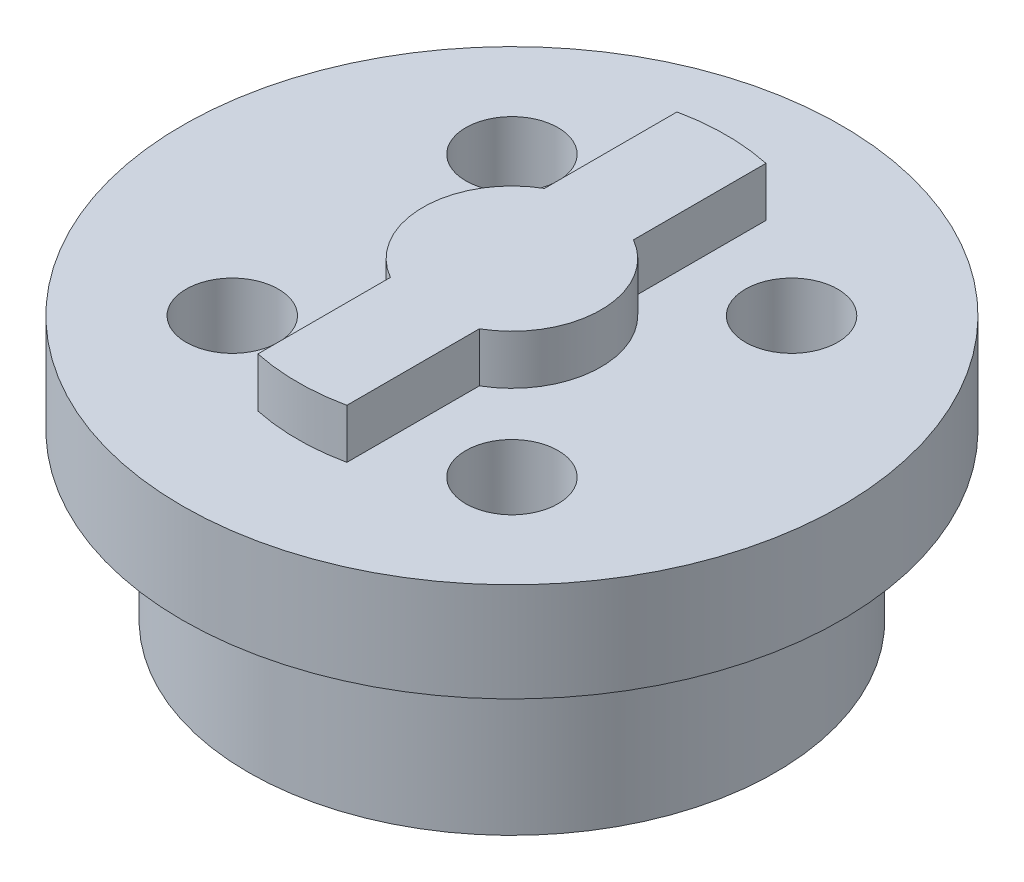
SolidWorks part; units mm, degrees
ref_plane "Front Plane" through (0, 0, 0) normal (0, 0, 1) x (1, 0, 0)
ref_plane "Top Plane" through (0, 0, 0) normal (0, 1, 0) x (1, 0, 0)
ref_plane "Right Plane" through (0, 0, 0) normal (1, 0, 0) x (0, 0, -1)
sketch "Sketch1" plane through (0, 0, 0) normal (0, 1, 0) x (1, 0, 0)
  circle A0 centre (0, 0) radius 10
  dimension "D1" = 20
extrude "Boss-Extrude1" add sketch "Sketch1" along normal blind 8
sketch "Sketch4" plane through (0, 8, 0) normal (0, 1, 0) x (1, 0, 0)
  line L0 (-1.35, 6.3583) -> (-1.35, 2.3383)
  line L2 (1.35, 2.3383) -> (1.35, 6.3583)
  line L3 (-1.35, -2.3383) -> (-1.35, -6.3583)
  line L5 (1.35, -2.3383) -> (1.35, -6.3583)
  arc A0 (-1.35, 6.3583) -> (1.35, 6.3583) centre (0, 0) cw
  arc A2 (1.35, -2.3383) -> (1.35, 2.3383) centre (0, 0) ccw
  arc A8 (-1.35, -6.3583) -> (1.35, -6.3583) centre (0, 0) ccw
  arc A9 (-1.35, 2.3383) -> (-1.35, -2.3383) centre (0, 0) ccw
  circle A10 centre (0, 0) radius 6.5 construction
  dimension "D1" = 2.7
  dimension "D3" = 13
  dimension "D2" = 2.7
extrude "Boss-Extrude2" add sketch "Sketch4" along normal blind 1.5
sketch "Sketch5" plane through (0, 0, 0) normal (0, 1, 0) x (1, 0, 0)
  circle A0 centre (0, 0) radius 8
  circle A1 centre (0, 0) radius 10
  circle A2 centre (0, 0) radius 10 construction
  dimension "D1" = 16
extrude "Cut-Extrude1" cut sketch "Sketch5" along normal offset from surface (5 mm away) 3 up to face at (0, 8, 0)
sketch "Sketch6" plane through (0, 0, 0) normal (0, -1, 0) x (1, 0, 0)
  line L0 (0, 0) -> (4.2426, 4.2426) construction
  line L1 (-1000, 0) -> (49000, 0) construction
  circle A0 centre (0, 0) radius 6 construction
  circle A1 centre (4.2426, 4.2426) radius 1.4
  dimension "D1" = 12
  dimension "D2" = 45
  dimension "D3" = 2.8
extrude "Cut-Extrude2" cut sketch "Sketch6" against normal up to next (8 mm away)
pattern_circular "CirPattern1" count 4 over 360 about axis through (0, 0, 0) along (0, 1, 0) of "Cut-Extrude2"
